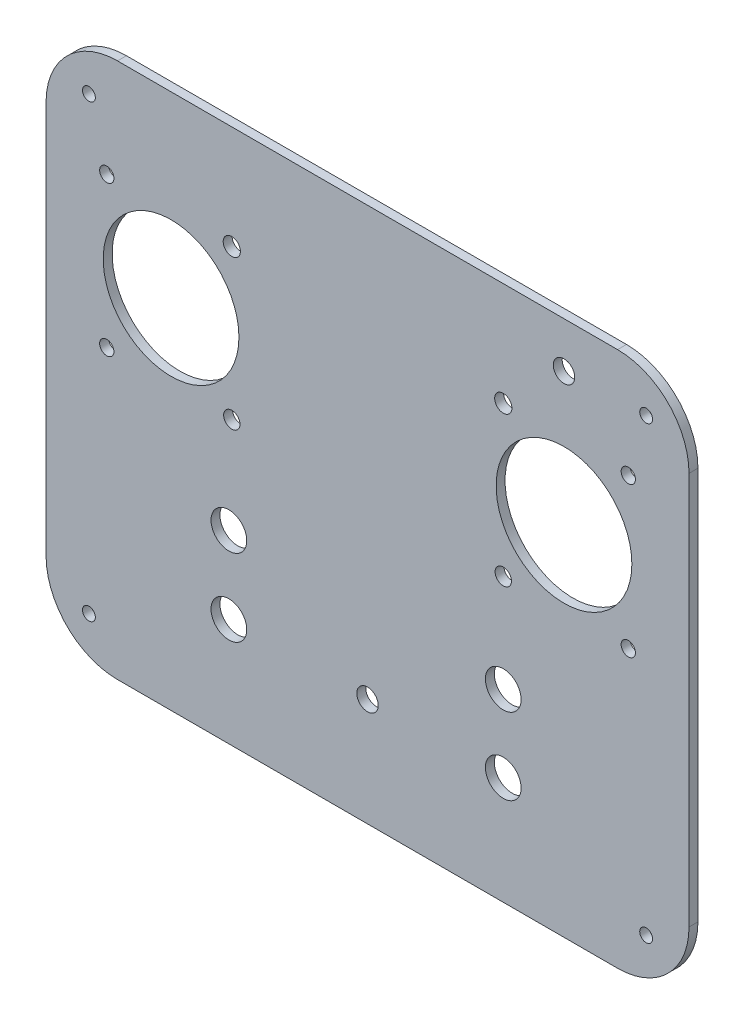
SolidWorks part; units mm, degrees
ref_plane "Front Plane" through (0, 0, 0) normal (0, 0, 1) x (1, 0, 0)
ref_plane "Top Plane" through (0, 0, 0) normal (0, 1, 0) x (1, 0, 0)
ref_plane "Right Plane" through (0, 0, 0) normal (1, 0, 0) x (0, 0, -1)
sketch "Sketch1" plane through (0, 0, 0) normal (0, 0, 1) x (1, 0, 0)
  line L0 (-53.9811, 61.6038) -> (-53.9811, 23.6038)
  line L1 (-88.9811, 92.6038) -> (91.0189, 92.6038)
  line L2 (-88.9811, 92.6038) -> (-88.9811, -57.3962)
  line L3 (-88.9811, -57.3962) -> (91.0189, -57.3962)
  line L4 (91.0189, 92.6038) -> (91.0189, -57.3962)
  line L5 (-34.9811, 42.6038) -> (-72.9811, 42.6038)
  circle A0 centre (-53.9811, 42.6038) radius 19
  circle A5 centre (-71.9811, 63.6038) radius 2
  circle A6 centre (-71.9811, 21.6038) radius 2
  circle A9 centre (-36.9811, 63.6038) radius 2.4122
  circle A10 centre (-36.9811, 21.6038) radius 2.2901
  circle A11 centre (39.0189, 63.6038) radius 2.4122
  circle A12 centre (74.0189, 63.6038) radius 2
  circle A13 centre (74.0189, 21.6038) radius 2
  circle A14 centre (39.0189, 21.6038) radius 2.2901
  circle A15 centre (56.0189, 42.6038) radius 19
  circle A16 centre (-37.798, -27.207) radius 5
  circle A17 centre (-37.798, -5.6376) radius 5
  circle A18 centre (39.0189, -5.7605) radius 5
  circle A20 centre (1.0189, -27.207) radius 3
  circle A21 centre (39.0189, -27.207) radius 5
  circle A22 centre (56.0189, 79.8769) radius 3
  dimension "D3" = 38
  dimension "D4" = 10
  dimension "D14" = 4
  dimension "D11" = 6
  dimension "D6" = 10
  dimension "D16" = 6
  dimension "D1" = 180
  dimension "D2" = 150
  dimension "D5" = 35
  dimension "D7" = 27.3642
  dimension "D8" = 100
  dimension "D9" = 17
  dimension "D10" = 0
  dimension "D12" = 21
  dimension "D13" = 18
  dimension "D15" = 17
extrude "Boss-Extrude3" add sketch "Sketch1" along normal blind 2.5 contours L4 L1 L2 L3 A22 A21 A20 A18 A17 A16 A14 A13 A11 A10 A9 A0 A5 A6 A12 A15
fillet "Fillet2" radius 20 4 edges at (-88.9811, 92.6038, 1.25) (91.0189, 92.6038, 1.25) (-88.9811, -57.3962, 1.25) (91.0189, -57.3962, 1.25)
sketch "Sketch2" plane through (0, 0, 2.5) normal (0, 0, 1) x (1, 0, 0)
  line L0 (-68.9811, -57.3962) -> (71.0189, -57.3962) construction
  line L1 (-88.9811, 72.6038) -> (-88.9811, -37.3962) construction
  line L2 (1.0189, -57.3962) -> (1.0189, 92.6038)
  line L3 (-68.9811, 92.6038) -> (71.0189, 92.6038) construction
  line L4 (-88.9811, 17.6038) -> (91.0189, 17.6038)
  line L5 (91.0189, 72.6038) -> (91.0189, -37.3962) construction
  circle A0 centre (-76.9811, -45.3962) radius 1.8
  circle A2 centre (79.0189, -45.3962) radius 1.8
  circle A3 centre (-76.9811, 80.6038) radius 1.8
  circle A4 centre (79.0189, 80.6038) radius 1.8
  point P20 (0, 0)
  dimension "D3" = 3.6
  dimension "D1" = 12
  dimension "D2" = 12
extrude "Cut-Extrude1" cut sketch "Sketch2" against normal up to next contours A4 | A2 | A0 | A3
